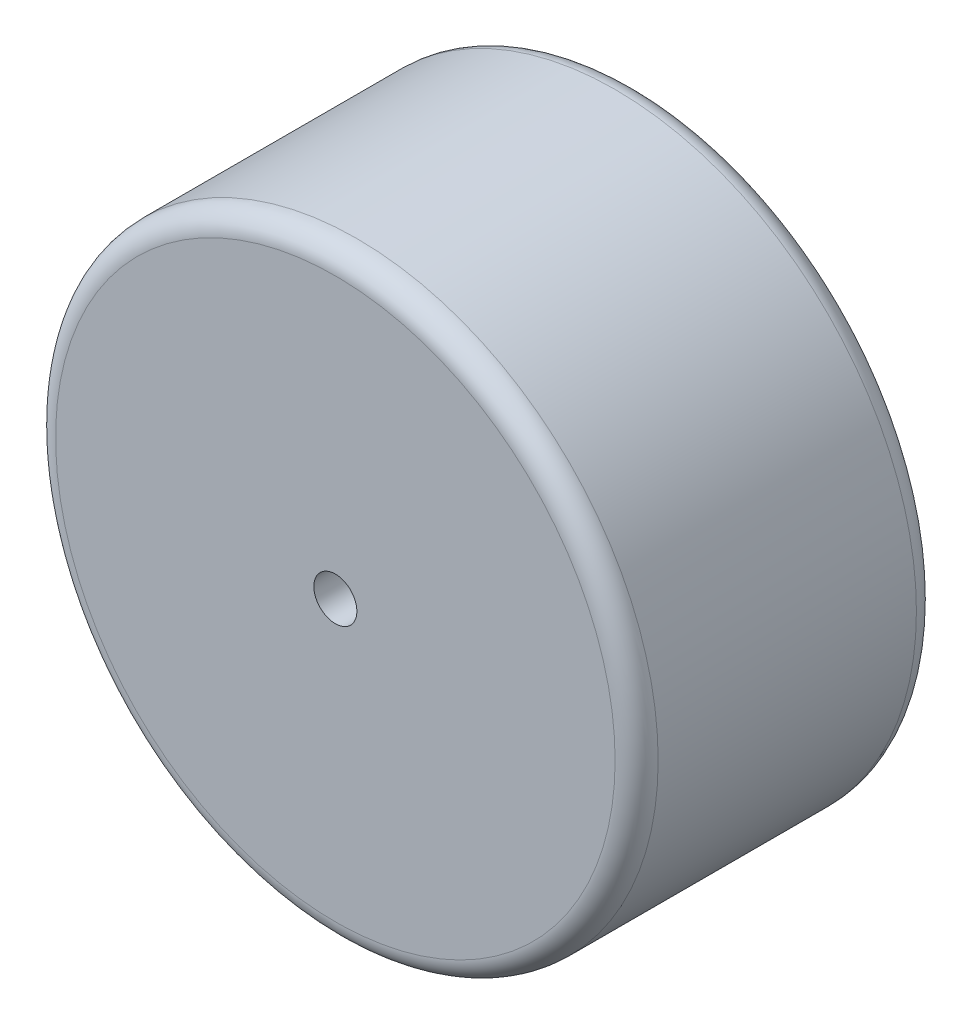
SolidWorks part; units mm, degrees
material "Rubber"
ref_plane "Front Plane" through (0, 0, 0) normal (0, 0, 1) x (1, 0, 0)
ref_plane "Top Plane" through (0, 0, 0) normal (0, 1, 0) x (1, 0, 0)
ref_plane "Right Plane" through (0, 0, 0) normal (1, 0, 0) x (0, 0, -1)
sketch "Sketch1" plane through (0, 0, 0) normal (0, 0, 1) x (1, 0, 0)
  circle A0 centre (0, 0) radius 88.9
  circle A1 centre (0, 0) radius 6.35
  dimension "D1" = 177.8
  dimension "D2" = 12.7
extrude "Boss-Extrude1" add sketch "Sketch1" along normal blind 88.9
fillet "Fillet1" radius 6.35 2 edges at (88.9, 0, 0) (88.9, 0, 88.9)
